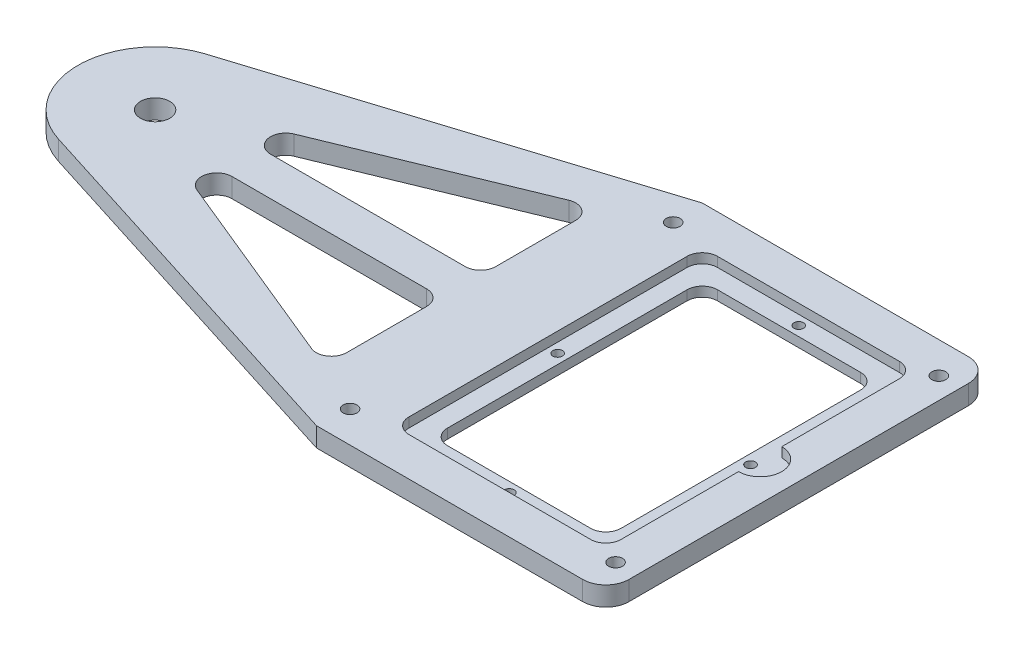
SolidWorks part; units mm, degrees
material "UHMW"
ref_plane "Front Plane" through (0, 0, 0) normal (0, 0, 1) x (1, 0, 0)
ref_plane "Top Plane" through (0, 0, 0) normal (0, 1, 0) x (1, 0, 0)
ref_plane "Right Plane" through (0, 0, 0) normal (1, 0, 0) x (0, 0, -1)
sketch "Sketch1" plane through (0, 0, 0) normal (0, 1, 0) x (1, 0, 0)
  line L0 (-47.625, 0) -> (47.625, 0) construction
  line L1 (-47.625, -63.5) -> (47.625, -63.5)
  line L2 (-47.625, -63.5) -> (-47.625, 63.5)
  line L3 (-47.625, 63.5) -> (47.625, 63.5)
  line L4 (47.625, -63.5) -> (47.625, 63.5)
  line L5 (-47.625, -63.5) -> (47.625, 63.5) construction
  line L6 (-47.625, 63.5) -> (47.625, -63.5) construction
  point P0 (0, 0)
  dimension "D1" = 95.25
  dimension "D2" = 127
  dimension "D3" = 63.5
extrude "Boss-Extrude1" add sketch "Sketch1" along normal blind 6.35
sketch "Sketch4" plane through (0, 6.35, 0) normal (0, 1, 0) x (1, 0, 0)
  line L1 (-47.625, 63.5) -> (-171.916, 24.2193)
  line L5 (-47.625, 63.5) -> (-47.625, -63.5) construction
  line L9 (-47.625, -63.5) -> (-171.916, -24.2193)
  line L10 (-47.625, 63.5) -> (-47.625, -63.5)
  arc A0 (-171.916, 24.2193) -> (-171.916, -24.2193) centre (-164.2618, 0) ccw
  circle A1 centre (-48.9458, 0) radius 2.5 construction
  dimension "D1" = 50.8
  dimension "D2" = 115.316
extrude "Boss-Extrude3" add sketch "Sketch4" against normal blind 6.35
sketch "Sketch5" plane through (0, 6.35, 0) normal (0, 1, 0) x (1, 0, 0)
  circle A0 centre (-164.2618, 0) radius 4.826
  circle A1 centre (-8.6868, 0) radius 4.826
  arc A2 (-171.916, 24.2193) -> (-171.916, -24.2193) centre (-164.2618, 0) ccw construction
  arc A3 (-171.916, 24.2193) -> (-171.916, -24.2193) centre (-164.2618, 0) ccw
  dimension "D1" = 9.652
  dimension "D2" = 155.575
extrude "Cut-Extrude1" cut sketch "Sketch5" against normal through all contours A0 | A1
sketch "Sketch6" plane through (0, 6.35, 0) normal (0, 1, 0) x (1, 0, 0)
  line L0 (-63.5, 6.35) -> (-63.5, -6.35) construction
  line L1 (-63.5, 45.1637) -> (-157.9118, 6.35)
  line L2 (-157.9118, 6.35) -> (-63.5, 6.35)
  line L3 (-63.5, 6.35) -> (-63.5, 45.1637)
  line L4 (-63.5, -6.35) -> (-63.5, -45.1637)
  line L5 (-63.5, -45.1637) -> (-157.9118, -6.35)
  line L6 (-157.9118, -6.35) -> (-63.5, -6.35)
  line L7 (0, 0) -> (-63.5, 0) construction
  line L8 (-47.625, 63.5) -> (-171.916, 24.2193) construction
  line L9 (-189.6618, 78.2466) -> (-189.6618, -78.2466) construction
  arc A1 (-171.916, 24.2193) -> (-171.916, -24.2193) centre (-164.2618, 0) ccw construction
  point P10 (-189.6618, 0)
  dimension "D1" = 12.7
  dimension "D2" = 31.75
  dimension "D3" = 12.7
  dimension "D4" = 63.5
extrude "Cut-Extrude2" cut sketch "Sketch6" against normal through all
fillet "Fillet9" radius 5 6 edges at (-157.9118, 3.175, 6.35) (-63.5, 3.175, 6.35) (-63.5, 3.175, 45.1637) (-63.5, 3.175, -6.35) (-157.9118, 3.175, -6.35) (-63.5, 3.175, -45.1637)
sketch "Sketch7" plane through (0, 6.35, 0) normal (0, 1, 0) x (1, 0, 0)
  circle A0 centre (-8.6868, 0) radius 5.4538
extrude "Boss-Extrude4" add sketch "Sketch7" against normal blind 6.35
sketch "Sketch8" plane through (0, 6.35, 0) normal (0, 1, 0) x (1, 0, 0)
  line L4 (-47.625, -63.5) -> (47.625, -63.5) construction
  line L5 (-34.925, 50.8) -> (-34.925, -50.8)
  line L7 (-47.625, 63.5) -> (-47.625, -63.5) construction
  line L8 (-171.916, -24.2193) -> (-47.625, -63.5) construction
  line L10 (47.625, 50.8) -> (-47.625, 50.8)
  line L11 (34.925, 50.8) -> (-34.925, 50.8)
  line L13 (34.925, -63.5) -> (34.925, 63.5)
  line L14 (34.925, -50.8) -> (34.925, 50.8)
  line L15 (-34.925, 63.5) -> (-34.925, -63.5) construction
  line L16 (-47.625, -50.8) -> (47.625, -50.8)
  line L17 (-34.925, -50.8) -> (34.925, -50.8)
  dimension "D1" = 12.7
  dimension "D2" = 12.7
  dimension "D3" = 12.7
  dimension "D4" = 12.7
extrude "Cut-Extrude3" cut sketch "Sketch8" against normal blind 3.175
sketch "Sketch9" plane through (0, 3.175, 0) normal (0, 1, 0) x (1, 0, 0)
  line L14 (-28.575, -44.45) -> (28.575, -44.45)
  line L15 (28.575, -44.45) -> (28.575, 44.45)
  line L16 (-28.575, 44.45) -> (-28.575, -44.45)
  line L17 (28.575, 44.45) -> (-28.575, 44.45)
  line L18 (-28.575, -44.45) -> (28.575, -44.45)
  line L19 (28.575, -44.45) -> (28.575, 44.45)
  line L20 (-28.575, 44.45) -> (-28.575, -44.45)
  line L21 (28.575, 44.45) -> (-28.575, 44.45)
  dimension "D1" = 6.35
extrude "Cut-Extrude4" cut sketch "Sketch9" against normal through all
sketch "Sketch11" plane through (0, 3.175, 0) normal (0, 1, 0) x (1, 0, 0)
  line L0 (0, 50.8) -> (0, -50.8) construction
  line L1 (34.925, 50.8) -> (-34.925, 50.8) construction
  line L2 (-34.925, -50.8) -> (34.925, -50.8) construction
  line L3 (-34.925, 0) -> (34.925, 0) construction
  line L4 (-34.925, 50.8) -> (-34.925, -50.8) construction
  line L5 (34.925, -50.8) -> (34.925, 50.8) construction
  line L6 (-34.925, 50.8) -> (-34.925, -50.8) construction
  line L7 (-28.575, 44.45) -> (-28.575, -44.45) construction
  line L8 (34.925, 50.8) -> (-34.925, 50.8) construction
  circle A0 centre (-31.75, 0) radius 1.5875
  circle A1 centre (31.75, 0) radius 1.5875
  circle A2 centre (0, 47.625) radius 1.5875
  circle A3 centre (0, -47.625) radius 1.5875
  dimension "D1" = 3.175
  dimension "D4" = 3.175
  dimension "D2" = 3.175
  dimension "D3" = 3.175
  dimension "D5" = 3.175
extrude "Cut-Extrude6" cut sketch "Sketch11" against normal through all
sketch "Sketch12" plane through (0, 6.35, 0) normal (0, 1, 0) x (1, 0, 0)
  line L0 (34.925, -50.8) -> (34.925, 50.8) construction
  line L1 (34.925, 7.112) -> (34.925, 50.8) construction
  line L2 (34.925, -7.112) -> (34.925, -50.8) construction
  line L3 (34.925, 0) -> (-34.925, 0) construction
  line L4 (-34.925, 50.8) -> (-34.925, -50.8) construction
  line L5 (34.925, -50.8) -> (34.925, 50.8) construction
  line L6 (34.925, 7.112) -> (34.925, -7.112)
  arc A0 (34.925, 7.112) -> (34.925, -7.112) centre (34.925, 0) cw
  dimension "D1" = 7.112
extrude "Cut-Extrude7" cut sketch "Sketch12" against normal blind 3.175
fillet "Fillet10" radius 5 4 edges at (-34.925, 4.7625, 50.8) (34.925, 4.7625, 50.8) (34.925, 4.7625, -50.8) (-34.925, 4.7625, -50.8)
fillet "Fillet11" radius 5 4 edges at (-28.575, 1.5875, -44.45) (28.575, 1.5875, -44.45) (28.575, 1.5875, 44.45) (-28.575, 1.5875, 44.45)
fillet "Fillet12" radius 7.62 2 edges at (47.625, 3.175, -63.5) (47.625, 3.175, 63.5)
sketch "Sketch13" plane through (0, 6.35, 0) normal (0, 1, 0) x (1, 0, 0)
  circle A0 centre (-46.8896, 53.1801) radius 2.2812
  circle A1 centre (-46.8896, -53.2002) radius 2.2812
  circle A2 centre (40.5396, -53.2204) radius 2.2812
  circle A3 centre (40.557, 53.1902) radius 2.2812
  circle A8 centre (-46.8896, 53.1801) radius 2.2812 construction
  circle A9 centre (40.557, 53.1902) radius 2.2812 construction
  circle A10 centre (40.5396, -53.2204) radius 2.2812 construction
  circle A11 centre (-46.8896, -53.2002) radius 2.2812 construction
extrude "Cut-Extrude8" cut sketch "Sketch13" against normal through all
